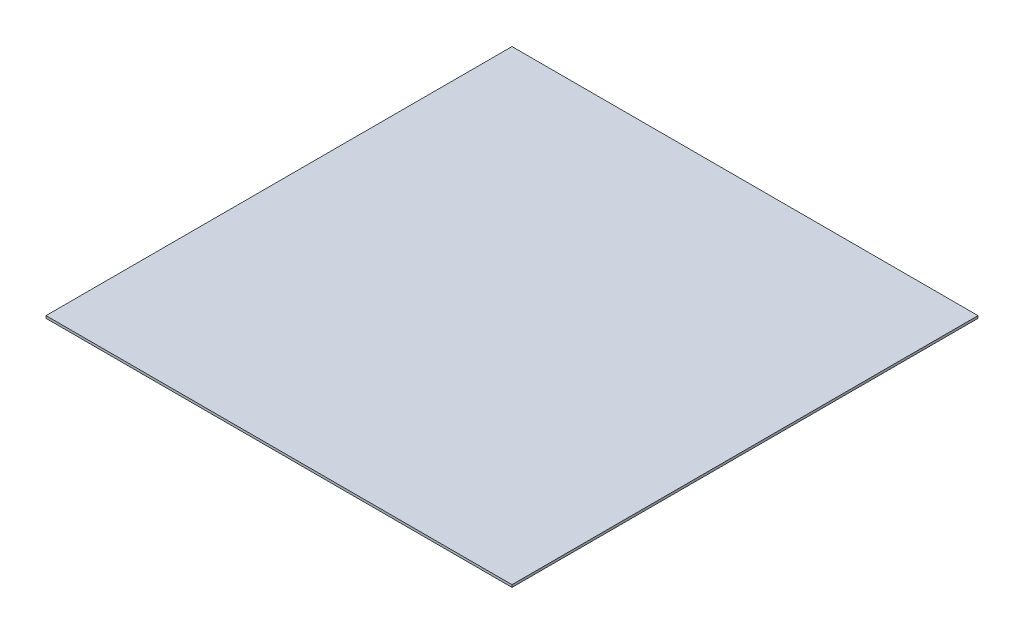
SolidWorks part; units mm, degrees
ref_plane "Front Plane" through (0, 0, 0) normal (0, 0, 1) x (1, 0, 0)
ref_plane "Top Plane" through (0, 0, 0) normal (0, 1, 0) x (1, 0, 0)
ref_plane "Right Plane" through (0, 0, 0) normal (1, 0, 0) x (0, 0, -1)
sketch "Sketch1" plane through (0, 0, 0) normal (0, 1, 0) x (1, 0, 0)
  line L1 (-76.2, -76.2) -> (76.2, -76.2)
  line L2 (-76.2, -76.2) -> (-76.2, 76.2)
  line L3 (-76.2, 76.2) -> (76.2, 76.2)
  line L4 (76.2, -76.2) -> (76.2, 76.2)
  line L5 (-76.2, -76.2) -> (76.2, 76.2) construction
  line L6 (-76.2, 76.2) -> (76.2, -76.2) construction
  point P0 (0, 0)
  dimension "D1" = 152.4
  dimension "D2" = 152.4
extrude "Boss-Extrude1" add sketch "Sketch1" along normal blind 0.7937 contours L4 L3 L2 L1
